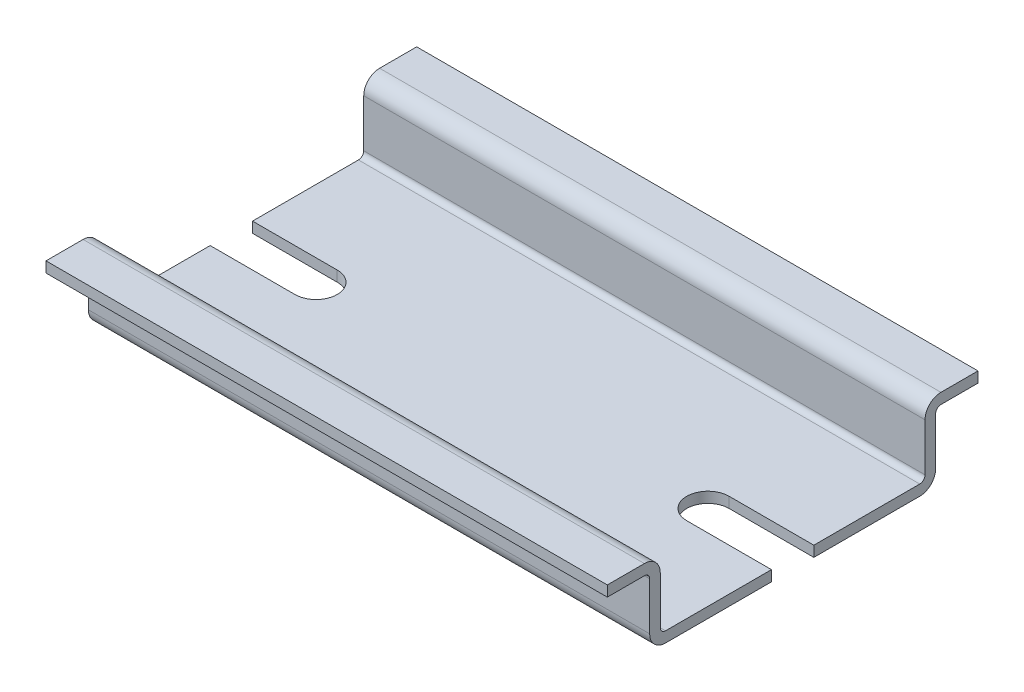
SolidWorks part; units mm, degrees
ref_plane "Front Plane" through (0, 0, 0) normal (0, 0, 1) x (1, 0, 0)
ref_plane "Top Plane" through (0, 0, 0) normal (0, 1, 0) x (1, 0, 0)
ref_plane "Right Plane" through (0, 0, 0) normal (1, 0, 0) x (0, 0, -1)
sketch "Sketch1" plane through (0, 0, 0) normal (1, 0, 0) x (0, 0, -1)
  line L0 (0, 0) -> (-12, 0)
  line L1 (-13.5, 1.5) -> (-13.5, 6)
  line L2 (-14, 6.5) -> (-17.5, 6.5)
  line L3 (-17.5, 6.5) -> (-17.5, 7.5)
  line L6 (-12, 1) -> (0, 1)
  line L7 (0, 1) -> (0, 0)
  line L8 (-12.5, 1.5) -> (-12.5, 6)
  line L9 (-14, 7.5) -> (-17.5, 7.5)
  arc A0 (-12, 0) -> (-13.5, 1.5) centre (-12, 1.5) cw
  arc A1 (-13.5, 6) -> (-14, 6.5) centre (-14, 6) ccw
  arc A3 (-12.5, 1.5) -> (-12, 1) centre (-12, 1.5) ccw
  arc A4 (-12.5, 6) -> (-14, 7.5) centre (-14, 6) ccw
  point P12 (0, 0.5)
  dimension "D5" = 0.5
  dimension "D1" = 7.5
  dimension "D2" = 1
  dimension "D3" = 12.5
  dimension "D4" = 17.5
extrude "Boss-Extrude1" add sketch "Sketch1" along normal blind 26.5
sketch "Sketch3" plane through (0, 1, 0) normal (0, 1, 0) x (1, 0, 0)
  line L6 (26.5, 0) -> (16.5, 0)
  line L7 (26.5, 0) -> (0, 0) construction
  line L8 (18.5, -2) -> (26.5, -2)
  line L9 (26.5, 0) -> (26.5, -12) construction
  line L10 (26.5, -2) -> (26.5, 0)
  line L11 (0, 0) -> (0, -12) construction
  arc A2 (16.5, 0) -> (18.5, -2) centre (18.5, 0) ccw
  dimension "D1" = 18.5
  dimension "D2" = 2
extrude "Cut-Extrude1" cut sketch "Sketch3" against normal through all
mirror "Mirror16" about plane through (0, 0, 0) normal (1, 0, 0) of "Cut-Extrude1", "Boss-Extrude1"
mirror "Mirror17" about plane through (0, 0, 0) normal (0, 0, 1) of "Mirror16", "Boss-Extrude1", "Cut-Extrude1"
